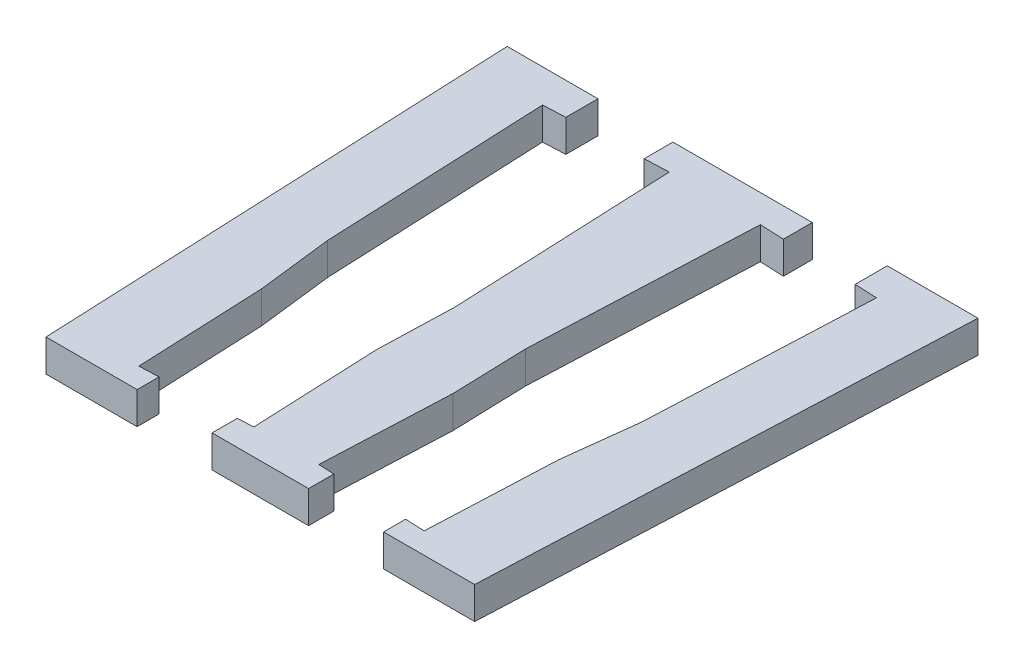
SolidWorks part; units mm, degrees
ref_plane "Front Plane" through (0, 0, 0) normal (0, 0, 1) x (1, 0, 0)
ref_plane "Top Plane" through (0, 0, 0) normal (0, 1, 0) x (1, 0, 0)
ref_plane "Right Plane" through (0, 0, 0) normal (1, 0, 0) x (0, 0, -1)
sketch "Sketch1" plane through (0, 0, 0) normal (0, 1, 0) x (1, 0, 0)
  line L0 (-21.9647, 100) -> (-20, 55)
  line L5 (-21.9647, 100) -> (0, 100)
  line L6 (0, 100) -> (0, 55)
  line L7 (0, 55) -> (-20, 55)
  point P4 (0, 77.5)
  dimension "D1" = 45
  dimension "D2" = 77.5
  dimension "D3" = 2.5
  dimension "D4" = 20
extrude "Boss-Extrude1" add sketch "Sketch1" along normal blind 3
sketch "Sketch2" plane through (0, 3, 0) normal (0, 1, 0) x (1, 0, 0)
  line L1 (-13.8373, 56.9506) -> (-2.5081, 57.4453)
  line L2 (-13.8373, 56.9506) -> (-15.5821, 96.9126)
  line L3 (-15.5821, 96.9126) -> (-4.2529, 97.4072)
  line L4 (-2.5081, 57.4453) -> (-4.2529, 97.4072)
  line L5 (-13.8373, 56.9506) -> (-4.2529, 97.4072) construction
  line L6 (-15.5821, 96.9126) -> (-2.5081, 57.4453) construction
  line L7 (-21.9647, 100) -> (-20, 55) construction
  point P0 (-9.0451, 77.1789)
  point P8 (-3.3805, 77.4262)
  dimension "D1" = 11.34
  dimension "D2" = 40
  dimension "D3" = 77.5
extrude "Cut-Extrude1" cut sketch "Sketch2" against normal through all both and the other way through all
ref_plane "Plane1" through (-5.6646, 0, 0.2473) normal (0.999, 0, -0.0436) x (-0.0436, 0, -0.999)
sketch "Sketch6" plane through (0, 3, 0) normal (0, 1, 0) x (1, 0, 0)
  line L0 (-13.8373, 56.9506) -> (-13.3128, 56.9735)
  line L1 (-2.5081, 57.4453) -> (-13.8373, 56.9506) construction
  line L2 (-13.3128, 56.9735) -> (-13.8363, 68.9621)
  line L3 (-13.8363, 68.9621) -> (-14.6661, 75.9325)
  line L4 (-13.8373, 56.9506) -> (-15.5821, 96.9126) construction
  line L5 (-14.6661, 75.9325) -> (-13.8373, 56.9506)
  dimension "D1" = 12
  dimension "D2" = 19
  dimension "D3" = 0.525
extrude "Boss-Extrude2" add sketch "Sketch6" against normal blind 3
mirror "Mirror3" about plane through (-5.6646, 0, 0.2473) normal (0.999, 0, -0.0436) of "Boss-Extrude2"
mirror "Mirror4" about plane through (0, 0, 0) normal (1, 0, 0) of "Mirror3", "Boss-Extrude2", "Cut-Extrude1", "Boss-Extrude1"
sketch "Sketch7" plane through (0, 3, 0) normal (0, 1, 0) x (1, 0, 0)
  line L0 (-13.5, 100) -> (-13.5, 97.0035)
  line L1 (21.9647, 100) -> (-21.9647, 100) construction
  line L2 (-15.5821, 96.9126) -> (-4.2529, 97.4072) construction
  line L3 (-13.5, 97.0035) -> (-6.5, 97.3091)
  line L4 (-6.5, 97.3091) -> (-6.5, 100)
  line L5 (-6.5, 100) -> (-13.5, 100)
  line L6 (21.9647, 100) -> (-21.9647, 100) construction
  point P11 (0, 100)
  dimension "D1" = 6.5
  dimension "D2" = 7
extrude "Cut-Extrude7" cut sketch "Sketch7" against normal through all both and the other way through all
sketch "Sketch13" plane through (0, 3, 0) normal (0, 1, 0) x (1, 0, 0)
  line L0 (6.5, 97.3091) -> (6.5, 100)
  line L1 (15.5821, 96.9126) -> (4.2529, 97.4072) construction
  line L2 (21.9647, 100) -> (-6.5, 100) construction
  line L3 (6.5, 100) -> (13.5, 100)
  line L4 (13.5, 100) -> (13.5, 97.0035)
  line L5 (13.5, 97.0035) -> (6.5, 97.3091)
  dimension "D1" = 7
  dimension "D2" = 13
extrude "Cut-Extrude8" cut sketch "Sketch13" against normal through all both and the other way through all
sketch "Sketch14" plane through (0, 3, 0) normal (0, 1, 0) x (1, 0, 0)
  line L0 (-11.5, 57.0527) -> (-11.5, 55)
  line L1 (-3.0326, 57.4224) -> (-13.3128, 56.9735) construction
  line L2 (-20, 55) -> (20, 55) construction
  line L3 (-11.5, 55) -> (-4.5, 55)
  line L4 (-4.5, 55) -> (-4.5, 57.3583)
  line L5 (-4.5, 57.3583) -> (-11.5, 57.0527)
  point P6 (0, 55)
  dimension "D1" = 7
  dimension "D2" = 4.5
extrude "Cut-Extrude9" cut sketch "Sketch14" against normal through all both and the other way through all
sketch "Sketch15" plane through (0, 3, 0) normal (0, 1, 0) x (1, 0, 0)
  line L0 (4.5, 57.3583) -> (4.5, 55)
  line L1 (3.0326, 57.4224) -> (13.3128, 56.9735) construction
  line L2 (-4.5, 55) -> (20, 55) construction
  line L3 (4.5, 55) -> (11.5, 55)
  line L4 (11.5, 55) -> (11.5, 57.0527)
  line L5 (11.5, 57.0527) -> (4.5, 57.3583)
  dimension "D1" = 7
  dimension "D2" = 9
extrude "Cut-Extrude10" cut sketch "Sketch15" against normal through all both and the other way through all
